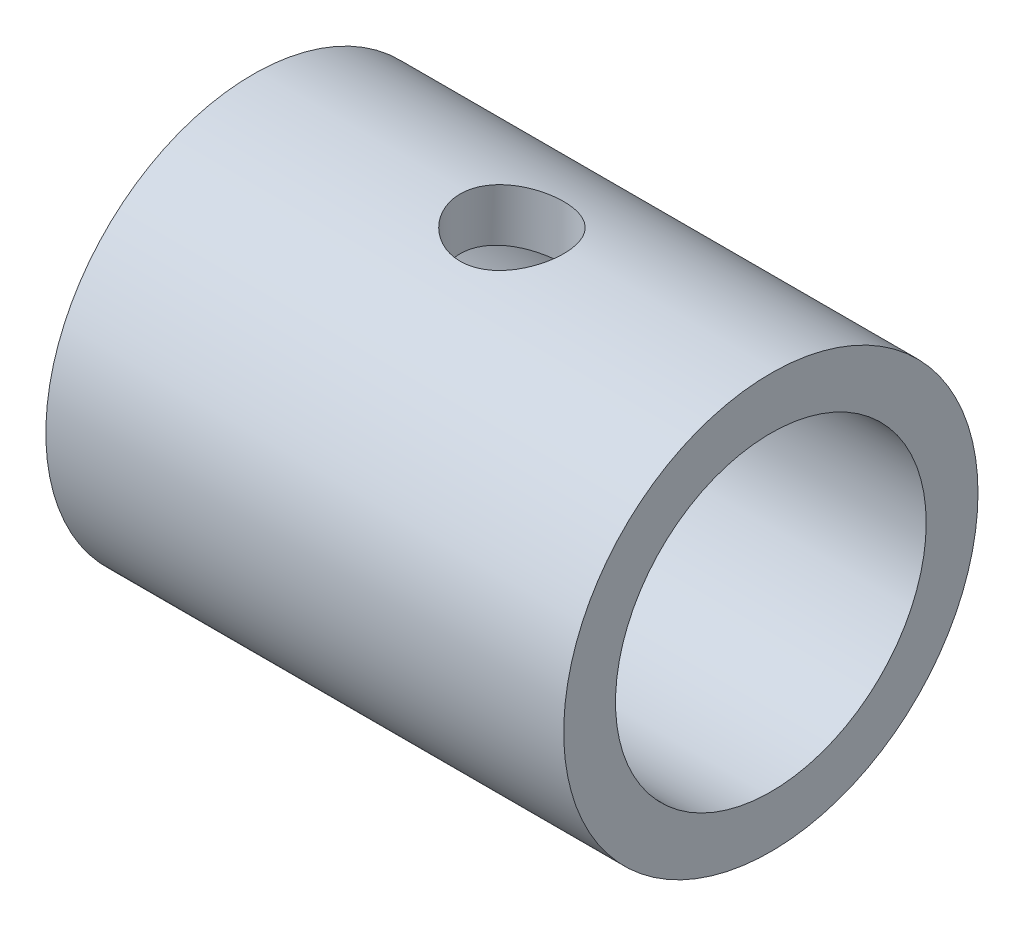
SolidWorks part; units mm, degrees
ref_plane "Front Plane" through (0, 0, 0) normal (0, 0, 1) x (1, 0, 0)
ref_plane "Top Plane" through (0, 0, 0) normal (0, 1, 0) x (1, 0, 0)
ref_plane "Right Plane" through (0, 0, 0) normal (1, 0, 0) x (0, 0, -1)
sketch "Sketch1" plane through (0, 0, 0) normal (1, 0, 0) x (0, 0, -1)
  circle A0 centre (0, 0) radius 6
  circle A1 centre (0, 0) radius 8
  dimension "D1" = 12
  dimension "D2" = 16
extrude "Boss-Extrude1" add sketch "Sketch1" along normal mid plane 20
sketch "Sketch2" plane through (0, 0, 0) normal (0, 1, 0) x (1, 0, 0)
  circle A0 centre (0, 0) radius 2
  dimension "D1" = 4
extrude "Cut-Extrude1" cut sketch "Sketch2" against normal mid plane 20
